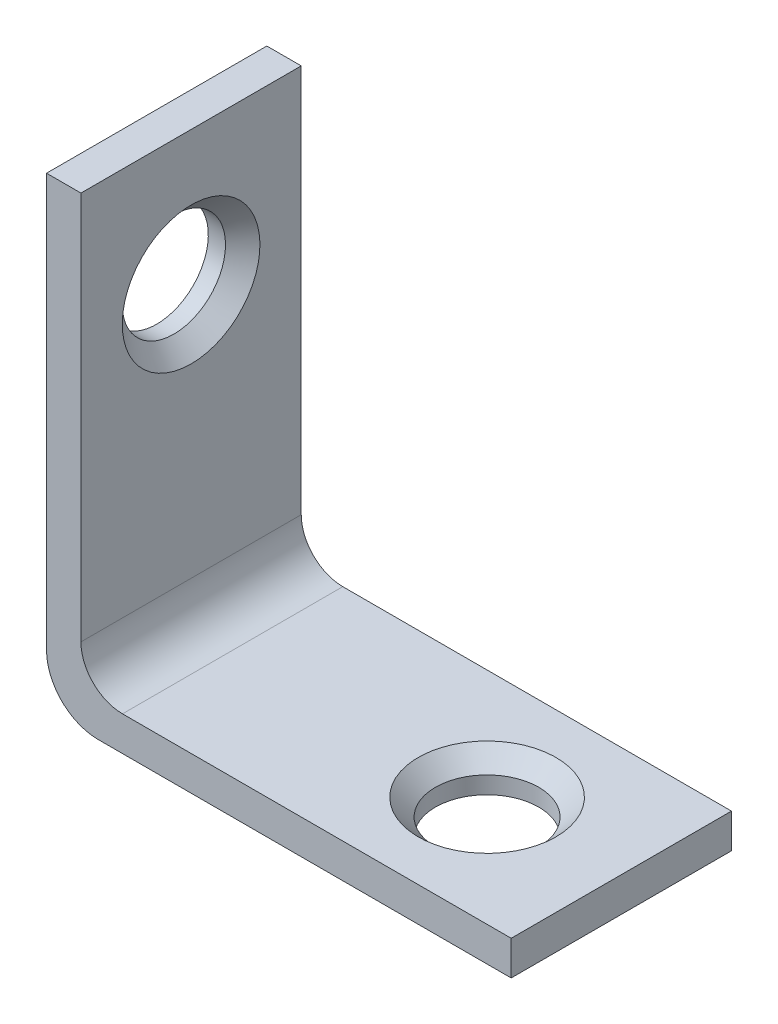
SolidWorks part; units mm, degrees
material "AISI 316 Stainless Steel Sheet (SS)"
ref_plane "Front Plane" through (0, 0, 0) normal (0, 0, 1) x (1, 0, 0)
ref_plane "Top Plane" through (0, 0, 0) normal (0, 1, 0) x (1, 0, 0)
ref_plane "Right Plane" through (0, 0, 0) normal (1, 0, 0) x (0, 0, -1)
sketch "Sketch1" plane through (0, 0, 0) normal (0, 0, 1) x (1, 0, 0)
  line L0 (0, 0) -> (3, 0) construction
  line L1 (3, 0) -> (27, 0)
  line L2 (0, 0) -> (0, 3) construction
  line L3 (0, 3) -> (0, 27)
  line L4 (27, 0) -> (27, 2)
  line L5 (2, 27) -> (2, 4.4142)
  line L6 (0, 27) -> (2, 27)
  line L7 (27, 2) -> (4.4142, 2)
  arc A0 (3, 0) -> (0, 3) centre (3, 3) cw
  arc A1 (2, 4.4142) -> (4.4142, 2) centre (4.4142, 4.4142) ccw
  dimension "D3" = 3
  dimension "D1" = 2
  dimension "D4" = 2
  dimension "D2" = 27
extrude "Boss-Extrude1" add sketch "Sketch1" along normal mid plane 12.8
sketch "Sketch2" plane through (0, 2, 0) normal (0, 1, 0) x (1, 0, 0)
  line L0 (27, 0) -> (19.2, 0) construction
  line L1 (27, -6.4) -> (27, 6.4) construction
  circle A0 centre (19.2, 0) radius 3
  dimension "D2" = 6
  dimension "D1" = 7.8
sketch "Sketch3" plane through (2, 0, 0) normal (1, 0, 0) x (0, 0, -1)
  line L0 (0, 27) -> (0, 19.2) construction
  line L1 (-6.4, 27) -> (6.4, 27) construction
  circle A0 centre (0, 19.2) radius 3
  dimension "D2" = 6
  dimension "D1" = 7.8
extrude "Cut-Extrude1" cut sketch "Sketch2" against normal through all
extrude "Cut-Extrude2" cut sketch "Sketch3" against normal through all
chamfer "Chamfer1" distance 1 angle 45 2 edges at (2, 22.2, 0) (16.2, 2, 0)
